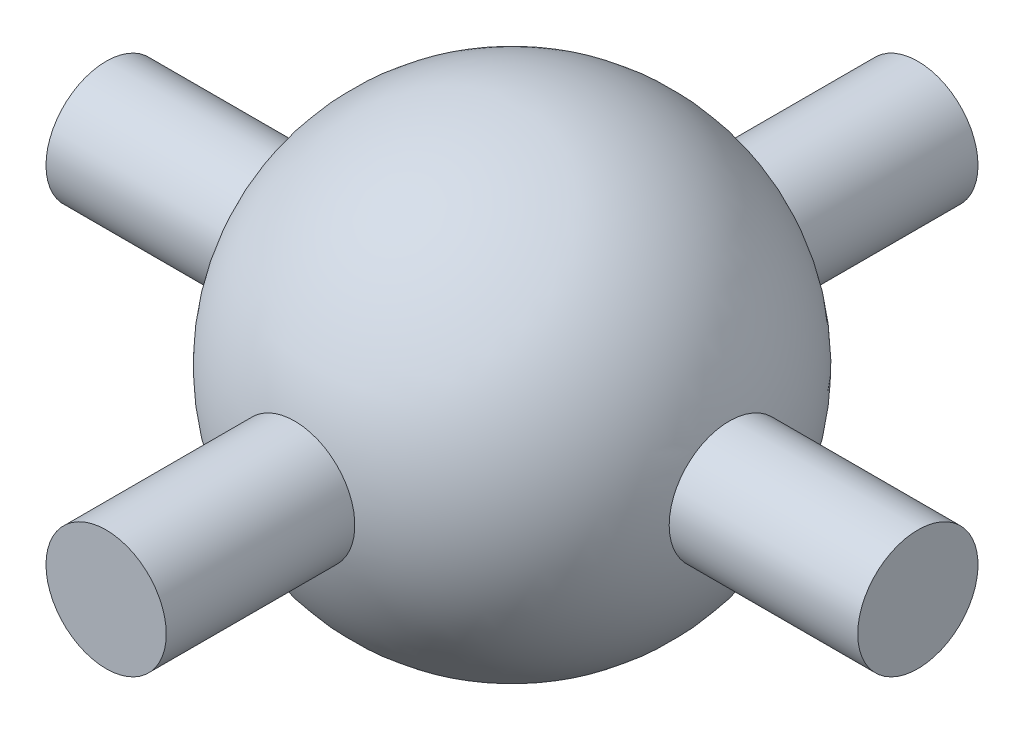
SolidWorks part; units mm, degrees
ref_plane "Front Plane" through (0, 0, 0) normal (0, 0, 1) x (1, 0, 0)
ref_plane "Top Plane" through (0, 0, 0) normal (0, 1, 0) x (1, 0, 0)
ref_plane "Right Plane" through (0, 0, 0) normal (1, 0, 0) x (0, 0, -1)
sketch "Sketch1" plane through (0, 0, 0) normal (0, 0, 1) x (1, 0, 0)
  line L0 (0, 3.75) -> (0, -3.75)
  arc A0 (0, 3.75) -> (0, -3.75) centre (0, 0) cw
  dimension "D1" = 3.75
ref_axis "Axis1" through (0, 4.125, 0) along (0, -1, 0)
revolve "Revolve2" add sketch "Sketch1" angle 360 about L0
sketch "Sketch2" plane through (0, 0, 0) normal (0, 0, 1) x (1, 0, 0)
  circle A0 centre (0, 0) radius 1
  dimension "D1" = 2
extrude "Boss-Extrude1" add sketch "Sketch2" along normal mid plane 13.5
pattern_circular "CirPattern1" count 2 over 90 about axis through (0, 4.125, 0) along (0, -1, 0) of "Boss-Extrude1"
